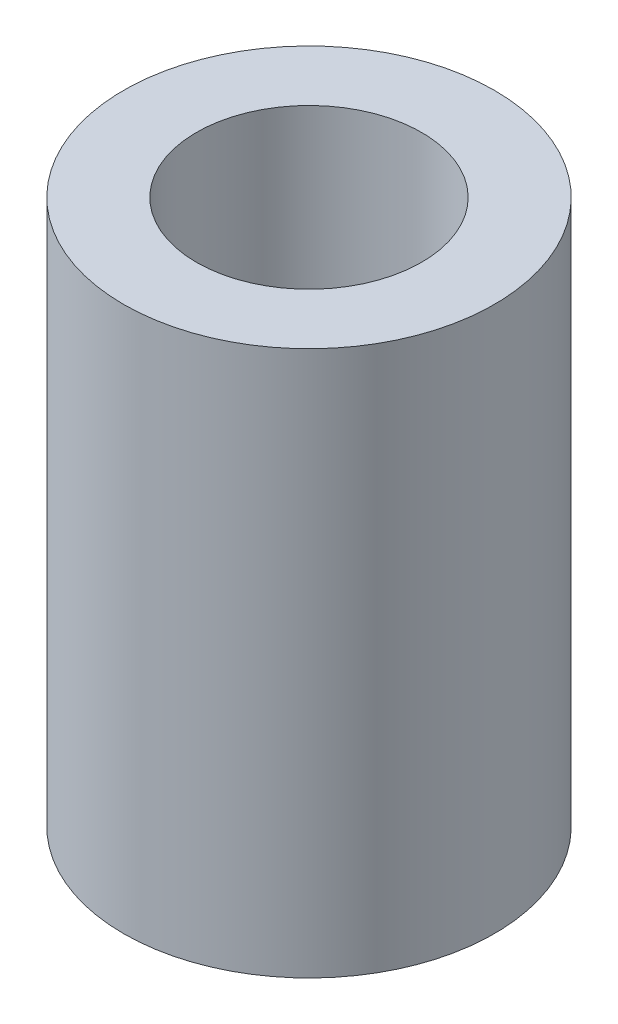
SolidWorks part; units mm, degrees
ref_plane "Front Plane" through (0, 0, 0) normal (0, 0, 1) x (1, 0, 0)
ref_plane "Top Plane" through (0, 0, 0) normal (0, 1, 0) x (1, 0, 0)
ref_plane "Right Plane" through (0, 0, 0) normal (1, 0, 0) x (0, 0, -1)
sketch "Sketch1" plane through (0, 0, 0) normal (0, 1, 0) x (1, 0, 0)
  circle A0 centre (0, 0) radius 4.25
  circle A1 centre (0, 0) radius 7
  dimension "D1" = 8.5
  dimension "D2" = 14
extrude "Boss-Extrude1" add sketch "Sketch1" along normal blind 20.575
